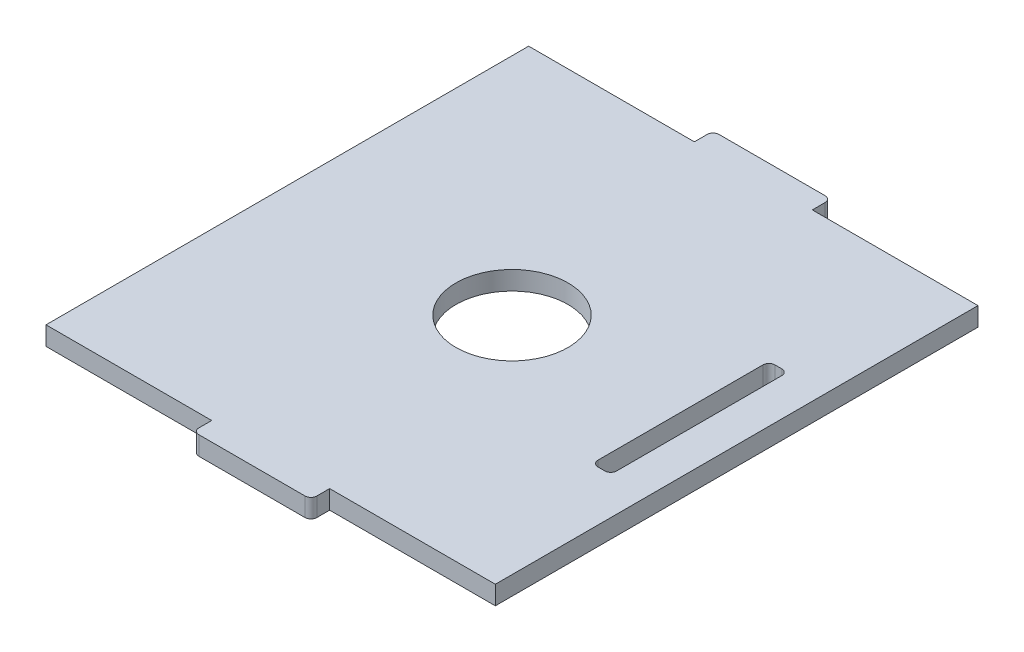
SolidWorks part; units mm, degrees
ref_plane "Front Plane" through (0, 0, 0) normal (0, 0, 1) x (1, 0, 0)
ref_plane "Top Plane" through (0, 0, 0) normal (0, 1, 0) x (1, 0, 0)
ref_plane "Right Plane" through (0, 0, 0) normal (1, 0, 0) x (0, 0, -1)
sketch "Sketch1" plane through (0, 0, 0) normal (0, 1, 0) x (1, 0, 0)
  line L0 (-10, 40.925) -> (10, 40.925) construction
  line L1 (-38.1, -40.925) -> (-10, -40.925)
  line L2 (-38.1, -40.925) -> (-38.1, 40.925)
  line L3 (-38.1, 40.925) -> (-10, 40.925)
  line L4 (38.1, -40.925) -> (38.1, 40.925)
  line L5 (-38.1, -40.925) -> (38.1, 40.925) construction
  line L6 (-38.1, 40.925) -> (38.1, -40.925) construction
  line L7 (-10, 40.925) -> (10, 40.925) construction
  line L8 (-10, 40.925) -> (-10, 44.1)
  line L9 (-10, 44.1) -> (10, 44.1)
  line L10 (10, 40.925) -> (10, 44.1)
  line L11 (10, 40.925) -> (38.1, 40.925)
  line L12 (0, 0) -> (-5.8133, 0) construction
  line L13 (10, -40.925) -> (10, -44.1)
  line L14 (-10, -44.1) -> (10, -44.1)
  line L15 (-10, -40.925) -> (-10, -44.1)
  line L16 (-10, -40.925) -> (10, -40.925) construction
  line L17 (10, -40.925) -> (38.1, -40.925)
  point P0 (0, 0)
  point P10 (-10, 42.5125)
  dimension "D1" = 76.2
  dimension "D2" = 81.85
  dimension "D3" = 20
  dimension "D4" = 3.175
extrude "Boss-Extrude1" add sketch "Sketch1" along normal blind 3.175
sketch "Sketch2" plane through (0, 3.175, 0) normal (0, 1, 0) x (1, 0, 0)
  line L0 (31.75, 40.925) -> (31.75, -40.925) construction
  line L1 (38.1, 40.925) -> (10, 40.925) construction
  line L2 (10, -40.925) -> (38.1, -40.925) construction
  line L3 (38.1, -40.925) -> (38.1, 40.925) construction
  line L4 (0, 0) -> (28.575, 0) construction
  line L5 (31.75, 0) -> (28.575, 0) construction
  line L6 (31.75, 15) -> (31.75, -15)
  line L7 (31.75, -15) -> (28.575, -15)
  line L8 (28.575, 15) -> (28.575, -15)
  line L9 (31.75, 15) -> (28.575, 15)
  line L10 (28.575, 0) -> (31.75, 0) construction
  line L11 (31.75, 0) -> (38.1, 0) construction
  circle A0 centre (0, 0) radius 9.5
  point P15 (30.1625, 0)
  dimension "D1" = 19
  dimension "D2" = 6.35
  dimension "D3" = 3.175
  dimension "D4" = 15
extrude "Cut-Extrude1" cut sketch "Sketch2" against normal through all
fillet "Fillet1" radius 1 8 edges at (28.575, 1.5875, -15) (31.75, 1.5875, -15) (28.575, 1.5875, 15) (31.75, 1.5875, 15) (10, 1.5875, 44.1) (-10, 1.5875, 44.1) (-10, 1.5875, -44.1) (10, 1.5875, -44.1)
